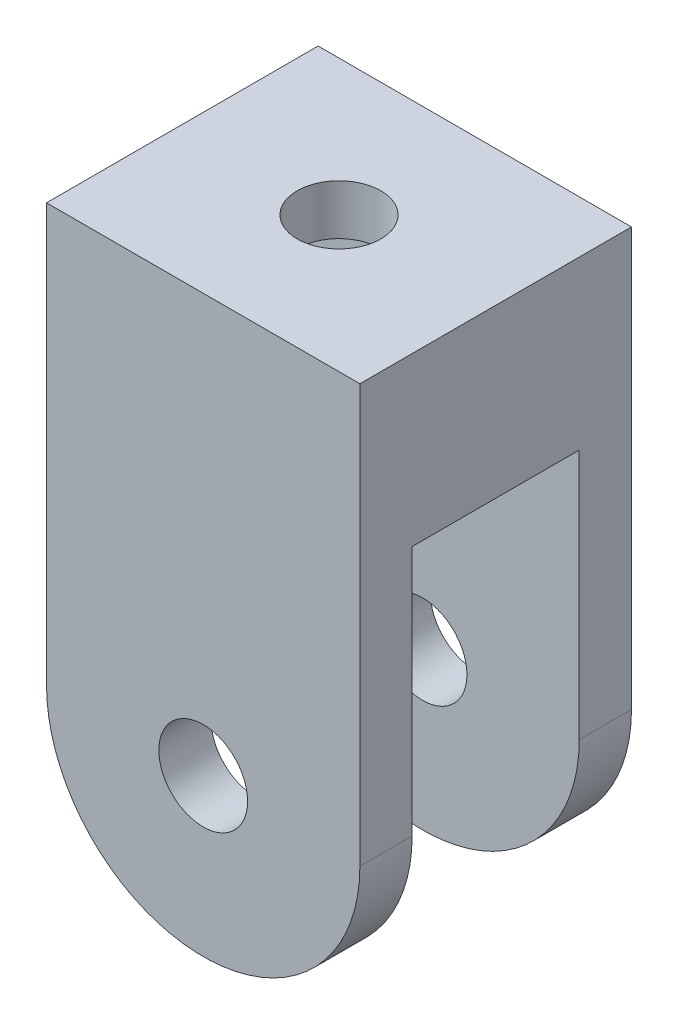
SolidWorks part; units mm, degrees
ref_plane "Front Plane" through (0, 0, 0) normal (0, 0, 1) x (1, 0, 0)
ref_plane "Top Plane" through (0, 0, 0) normal (0, 1, 0) x (1, 0, 0)
ref_plane "Right Plane" through (0, 0, 0) normal (1, 0, 0) x (0, 0, -1)
sketch "Sketch1" plane through (0, 0, 0) normal (0, 0, 1) x (1, 0, 0)
  line L2 (2.5, 10) -> (2.5, 30)
  line L3 (2.5, 30) -> (17.5, 30)
  line L4 (17.5, 10) -> (17.5, 30)
  line L5 (10, 30) -> (10, -5) construction
  line L6 (2.5, 10) -> (17.5, 10) construction
  arc A0 (2.5, 10) -> (17.5, 10) centre (10, 10) ccw
  circle A1 centre (10, 10) radius 2.125
  dimension "D3" = 4.25
  dimension "D1" = 20
  dimension "D2" = 7.5
extrude "Boss-Extrude1" add sketch "Sketch1" along normal blind 2.5
sketch "Sketch2" plane through (0, 0, 0) normal (0, 0, -1) x (-1, 0, 0)
  line L0 (-10, 30) -> (-10, 2.5) construction
  line L1 (-17.5, 30) -> (-2.5, 30) construction
  line L2 (-10, 2.5) -> (-10, 22.5) construction
  line L3 (-2.5, 30) -> (-2.5, 10) construction
  line L4 (-17.5, 30) -> (-2.5, 30)
  line L5 (-17.5, 30) -> (-17.5, 22)
  line L6 (-17.5, 22) -> (-2.5, 22)
  line L7 (-2.5, 30) -> (-2.5, 22)
  arc A0 (-17.5, 10) -> (-2.5, 10) centre (-10, 10) ccw construction
  dimension "D1" = 20
  dimension "D2" = 8
extrude "Boss-Extrude2" add sketch "Sketch2" along normal blind 8
ref_plane "Plane1" through (0, 0, -4) normal (0, 0, 1) x (1, 0, 0)
mirror "Mirror1" about plane through (0, 0, -4) normal (0, 0, 1) of "Boss-Extrude1"
sketch "Sketch4" plane through (0, 30, 0) normal (0, 1, 0) x (1, 0, 0)
  line L0 (10, 10.5) -> (10, -2.5) construction
  line L1 (17.5, 10.5) -> (2.5, 10.5) construction
  line L2 (17.5, -2.5) -> (2.5, -2.5) construction
  line L3 (2.5, 4) -> (17.5, 4) construction
  line L4 (2.5, -2.5) -> (2.5, 10.5) construction
  line L5 (17.5, -2.5) -> (17.5, 10.5) construction
  circle A0 centre (10, 4) radius 2
extrude "Cut-Extrude1" cut sketch "Sketch4" against normal up to next
sketch "Sketch5" plane through (0, 0, 2.5) normal (0, 0, 1) x (1, 0, 0)
  line L0 (10, 30) -> (10, 2.5) construction
  line L1 (17.5, 30) -> (2.5, 30) construction
  arc A0 (2.5, 10) -> (17.5, 10) centre (10, 10) ccw construction
sketch "Sketch6" plane through (2.5, 0, 0) normal (-1, 0, 0) x (0, 0, 1)
  line L0 (-4, 29.4005) -> (-4, 19.4005) construction
  line L9 (-7.5, 25.975) -> (2.5, 25.975) construction
  line L10 (2.5, 30) -> (-10.5, 30) construction
  line L11 (-7.625, 27.6) -> (-0.375, 27.6)
  line L12 (-7.625, 27.6) -> (-7.625, 24.35)
  line L13 (-7.625, 24.35) -> (-0.375, 24.35)
  line L14 (-0.375, 27.6) -> (-0.375, 24.35)
  line L15 (-8, 22) -> (0, 22) construction
  line L16 (2.5, 30) -> (2.5, 2.5) construction
  line L18 (-10.5, 10) -> (-10.5, 30) construction
  dimension "D1" = 7.25
  dimension "D2" = 3.25
  dimension "D3" = 3.625
  dimension "D4" = 3.625
  dimension "D5" = 1.625
  dimension "D6" = 1.625
  dimension "D7" = 2.4
  dimension "D8" = 2.35
  dimension "D9" = 2.875
  dimension "D10" = 2.875
extrude "Cut-Extrude2" cut sketch "Sketch6" against normal blind 11.5
